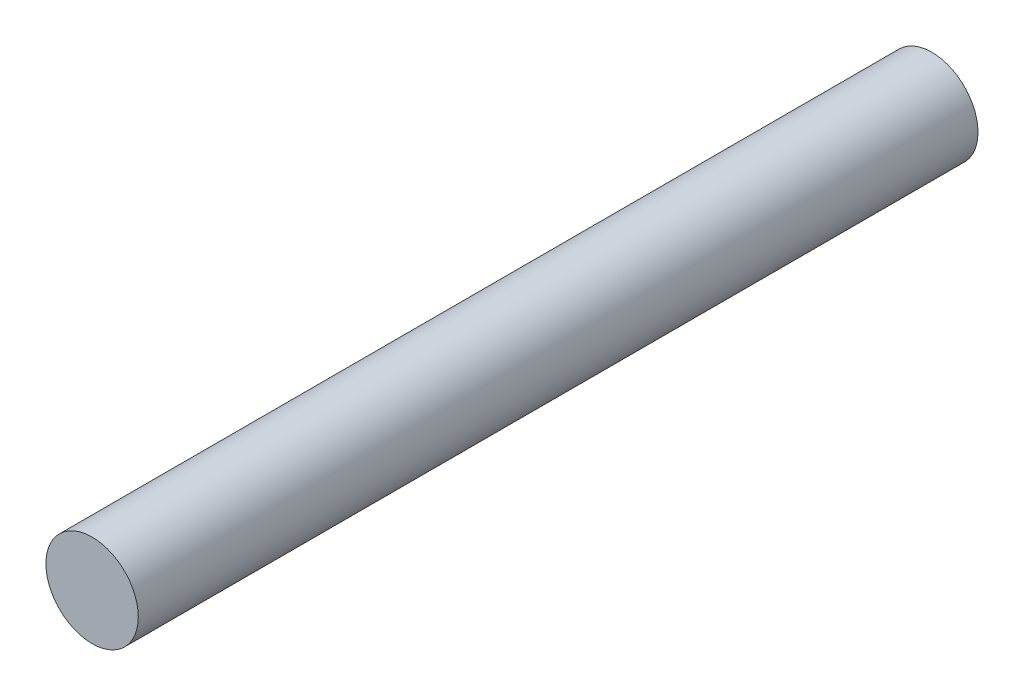
SolidWorks part; units mm, degrees
ref_plane "Přední rovina" through (0, 0, 0) normal (0, 0, 1) x (1, 0, 0)
ref_plane "Horní rovina" through (0, 0, 0) normal (0, 1, 0) x (1, 0, 0)
ref_plane "Pravá rovina" through (0, 0, 0) normal (1, 0, 0) x (0, 0, -1)
sketch "Skica1" plane through (0, 0, 0) normal (0, 0, 1) x (1, 0, 0)
  circle A0 centre (0, 0) radius 1.65
  dimension "D1" = 3.3
extrude "Přidat vysunutím1" add sketch "Skica1" along normal blind 30
